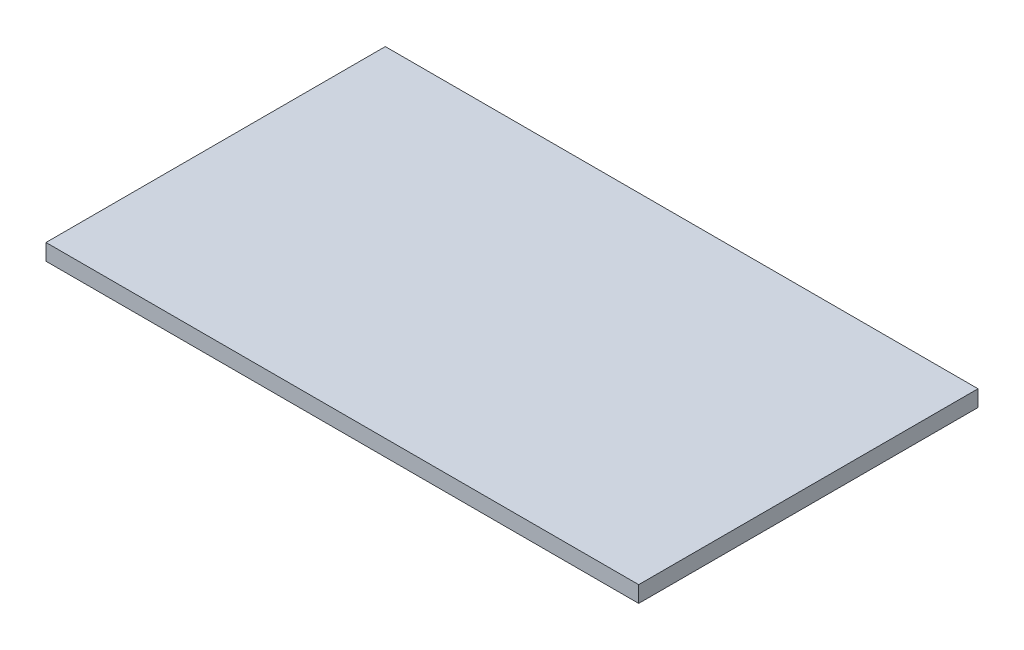
SolidWorks part; units mm, degrees
ref_plane "Front Plane" through (0, 0, 0) normal (0, 0, 1) x (1, 0, 0)
ref_plane "Top Plane" through (0, 0, 0) normal (0, 1, 0) x (1, 0, 0)
ref_plane "Right Plane" through (0, 0, 0) normal (1, 0, 0) x (0, 0, -1)
sketch "Sketch1" plane through (0, 0, 0) normal (0, 1, 0) x (1, 0, 0)
  line L24 (-54.619, 31.27) -> (54.619, -31.27) construction
  line L25 (54.619, 31.27) -> (-54.619, -31.27) construction
  line L28 (-54.619, 31.27) -> (-54.619, -31.27)
  line L29 (-54.619, -31.27) -> (54.619, -31.27)
  line L30 (54.619, -31.27) -> (54.619, 31.27)
  line L31 (54.619, 31.27) -> (-54.619, 31.27)
  point P0 (0, 0)
  point P2 (0, 0)
  point P4 (0, 0)
  dimension "D1" = 62.54
  dimension "D2" = 109.238
extrude "Boss-Extrude1" add sketch "Sketch1" along normal blind 3
sketch "Sketch2" plane through (0, 0, 0) normal (0, -1, 0) x (1, 0, 0)
  line L4 (53.119, -29.77) -> (53.119, 29.77) construction
  line L5 (53.119, 29.77) -> (-53.119, 29.77) construction
  line L6 (-53.119, 29.77) -> (-53.119, -29.77) construction
  line L7 (-53.119, -29.77) -> (53.119, -29.77) construction
  line L12 (-53.119, 29.77) -> (53.119, -29.77) construction
  line L13 (53.119, 29.77) -> (-53.119, -29.77) construction
  line L30 (53.619, 30.27) -> (-53.619, 30.27)
  line L31 (-53.619, 30.27) -> (-53.619, -30.27)
  line L32 (-53.619, -30.27) -> (53.619, -30.27)
  line L33 (53.619, -30.27) -> (53.619, 30.27)
  line L34 (52.619, 29.27) -> (-52.619, 29.27)
  line L35 (-52.619, 29.27) -> (-52.619, -29.27)
  line L36 (-52.619, -29.27) -> (52.619, -29.27)
  line L37 (52.619, -29.27) -> (52.619, 29.27)
  point P0 (-71.6732, 19.6158)
  point P12 (0, 0)
  point P13 (0, 0)
  point P14 (-29.1945, 34.3463)
  dimension "D1" = 106.238
  dimension "D2" = 59.54
  dimension "D3" = 0.5
  dimension "D4" = 0.5
extrude "Boss-Extrude2" add sketch "Sketch2" along normal blind 3 draft 45
